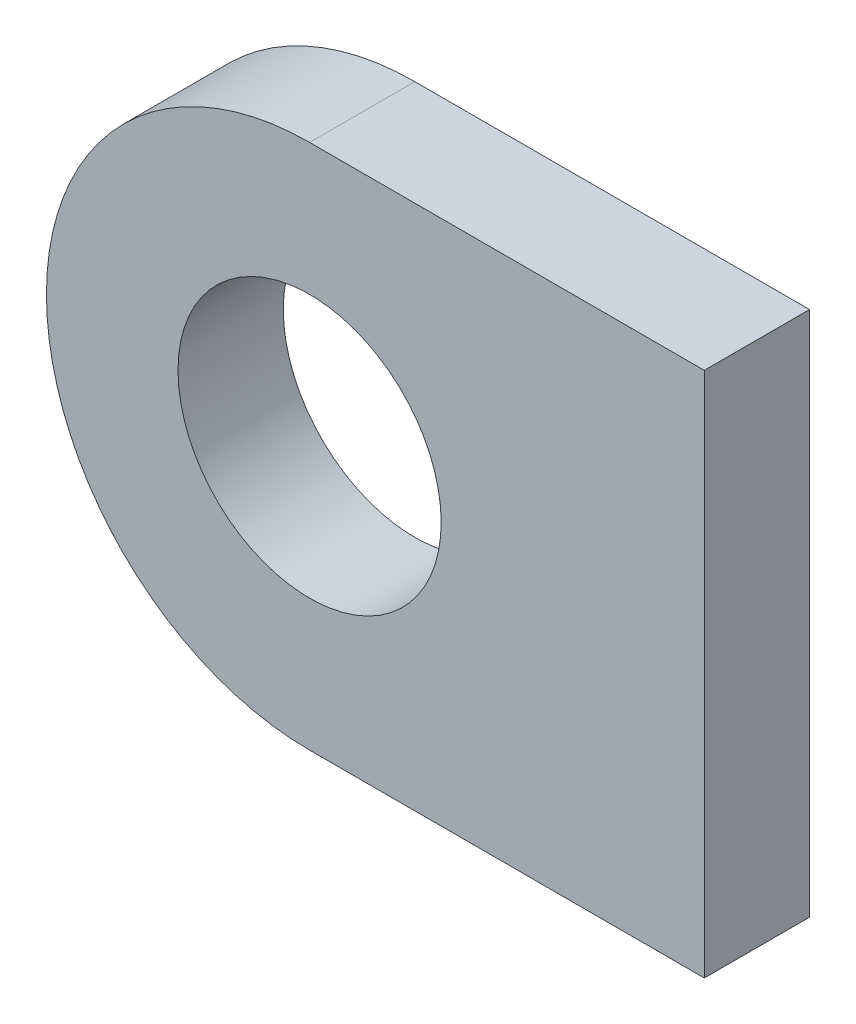
SolidWorks part; units mm, degrees
ref_plane "Спереди" through (0, 0, 0) normal (0, 0, 1) x (1, 0, 0)
ref_plane "Сверху" through (0, 0, 0) normal (0, 1, 0) x (1, 0, 0)
ref_plane "Справа" through (0, 0, 0) normal (1, 0, 0) x (0, 0, -1)
sketch "Эскиз1" plane through (0, 0, 0) normal (0, 0, 1) x (1, 0, 0)
  line L0 (0, 10) -> (15, 10)
  line L1 (15, 10) -> (15, -10)
  line L2 (15, -10) -> (0, -10)
  circle A0 centre (0, 0) radius 5
  circle A1 centre (0, 0) radius 10
  dimension "D1" = 10
  dimension "D2" = 5
  dimension "D3" = 15
extrude "Бобышка-Вытянуть1" add sketch "Эскиз1" along normal blind 4 contours A1 A0 | A1 L2 L1 L0
